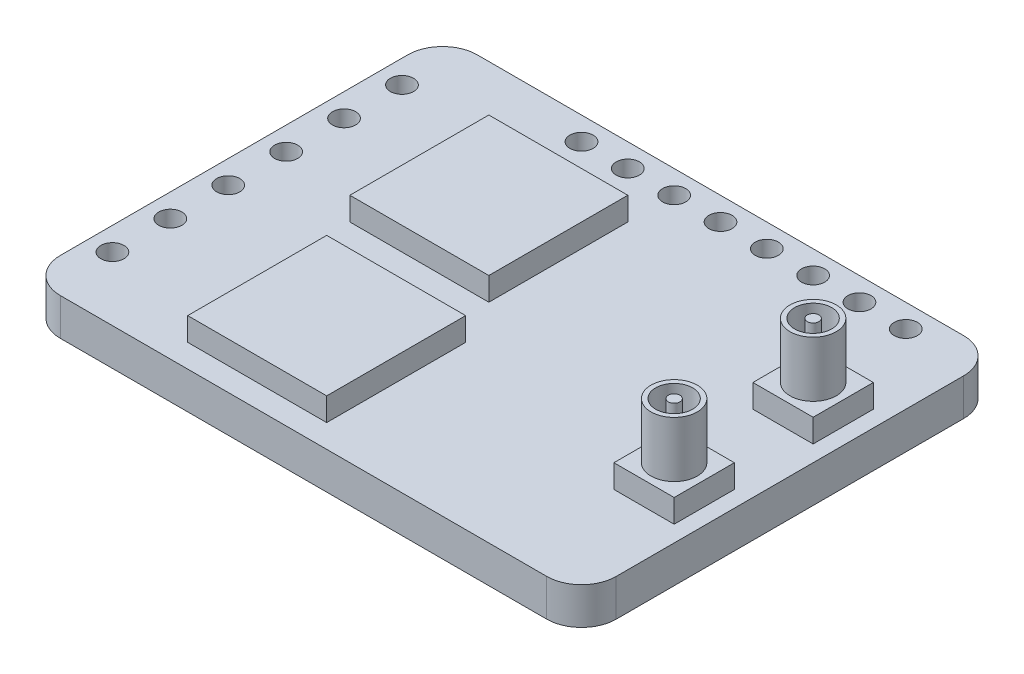
SolidWorks part; units mm, degrees
material "A-Glass Fiber"
ref_plane "Front Plane" through (0, 0, 0) normal (0, 0, 1) x (1, 0, 0)
ref_plane "Top Plane" through (0, 0, 0) normal (0, 1, 0) x (1, 0, 0)
ref_plane "Right Plane" through (0, 0, 0) normal (1, 0, 0) x (0, 0, -1)
sketch "Sketch1" plane through (0, 0, 0) normal (0, 1, 0) x (1, 0, 0)
  line L0 (-12, 0) -> (12, 0) construction
  line L1 (-12, -9) -> (12, -9) construction
  line L2 (-12, -9) -> (-12, 9) construction
  line L3 (-12, 9) -> (12, 9) construction
  line L4 (12, -9) -> (12, 9) construction
  line L5 (-12, -9) -> (12, 9) construction
  line L6 (-12, 9) -> (12, -9) construction
  line L7 (-12, 7.5) -> (-12, -7.5)
  line L8 (0, 9) -> (0, -9) construction
  line L9 (12, 7.5) -> (12, -7.5)
  line L10 (-10.5, 9) -> (10.5, 9)
  line L11 (-10.5, -9) -> (10.5, -9)
  arc A0 (-12, 7.5) -> (-10.5, 9) centre (-10.5, 7.5) cw
  arc A1 (-12, -7.5) -> (-10.5, -9) centre (-10.5, -7.5) ccw
  arc A2 (12, -7.5) -> (10.5, -9) centre (10.5, -7.5) cw
  arc A3 (12, 7.5) -> (10.5, 9) centre (10.5, 7.5) ccw
  circle A4 centre (-11, 6.25) radius 0.5
  circle A5 centre (-11, 3.75) radius 0.5
  circle A6 centre (-11, 1.25) radius 0.5
  circle A7 centre (-11, -1.25) radius 0.5
  circle A8 centre (-11, -3.75) radius 0.5
  circle A9 centre (-11, -6.25) radius 0.5
  circle A10 centre (9, 8) radius 0.5
  circle A11 centre (7, 8) radius 0.5
  circle A12 centre (5, 8) radius 0.5
  circle A13 centre (3, 8) radius 0.5
  circle A14 centre (1, 8) radius 0.5
  circle A15 centre (-1, 8) radius 0.5
  circle A16 centre (-3, 8) radius 0.5
  circle A17 centre (-5, 8) radius 0.5
  point P0 (0, 0)
  dimension "D3" = 1.5
  dimension "D4" = 1
  dimension "D8" = 1
  dimension "D1" = 24
  dimension "D2" = 18
  dimension "D5" = 1
  dimension "D6" = 2.75
  dimension "D9" = 1
  dimension "D10" = 3
  dimension "D7" = 6
  dimension "D11" = 8
extrude "Boss-Extrude1" add sketch "Sketch1" along normal blind 1.6
sketch "Sketch2" plane through (0, 1.6, 0) normal (0, 1, 0) x (1, 0, 0)
  line L0 (-12, 0) -> (12, 0) construction
  line L1 (-7, 6) -> (-1, 6)
  line L2 (-7, 6) -> (-7, 0)
  line L3 (-7, 0) -> (-1, 0)
  line L4 (-1, 6) -> (-1, 0)
  line L5 (-7, 6) -> (-1, 0) construction
  line L6 (-7, 0) -> (-1, 6) construction
  line L7 (0, 9) -> (0, -9) construction
  line L8 (-6, -8) -> (0, -8)
  line L9 (-6, -8) -> (-6, -2)
  line L10 (-6, -2) -> (0, -2)
  line L11 (0, -8) -> (0, -2)
  line L12 (-6, -8) -> (0, -2) construction
  line L13 (-6, -2) -> (0, -8) construction
  point P0 (-4, 3)
  point P7 (-3, -5)
  dimension "D1" = 6
  dimension "D2" = 1
  dimension "D3" = 2
extrude "Boss-Extrude2" add sketch "Sketch2" along normal blind 1 separate body
sketch "Sketch3" plane through (0, 1.6, 0) normal (0, 1, 0) x (1, 0, 0)
  line L0 (10, 3) -> (10, -3) construction
  line L1 (10, -3) -> (12, -3) construction
  line L2 (12, 7.5) -> (12, -7.5) construction
  line L3 (12, -3) -> (12, 3) construction
  line L4 (12, 3) -> (10, 3) construction
  line L6 (0, 0) -> (12, 0) construction
  line L7 (-12, 0) -> (12, 0) construction
  circle A0 centre (10, 3) radius 1
  circle A1 centre (10, 3) radius 0.8
  circle A2 centre (10, 3) radius 0.25
  circle A3 centre (10, -3) radius 1
  circle A4 centre (10, -3) radius 0.8
  circle A5 centre (10, -3) radius 0.25
  dimension "D1" = 2
  dimension "D2" = 1.6
  dimension "D3" = 0.5
  dimension "D4" = 2
  dimension "D5" = 1.6
  dimension "D6" = 0.5
  dimension "D7" = 6
  dimension "D8" = 3
  dimension "D9" = 2
extrude "Boss-Extrude3" add sketch "Sketch3" along normal blind 3.4 separate body contours A3 A4 | A5 | A0 A1 | A2
sketch "Sketch4" plane through (0, 1.6, 0) normal (0, 1, 0) x (1, 0, 0)
  line L1 (8.7, 4.3) -> (11.3, 4.3)
  line L2 (8.7, 4.3) -> (8.7, 1.7)
  line L3 (8.7, 1.7) -> (11.3, 1.7)
  line L4 (11.3, 4.3) -> (11.3, 1.7)
  line L5 (8.7, 4.3) -> (11.3, 1.7) construction
  line L6 (8.7, 1.7) -> (11.3, 4.3) construction
  line L7 (8.7, -1.7) -> (11.3, -1.7)
  line L8 (8.7, -1.7) -> (8.7, -4.3)
  line L9 (8.7, -4.3) -> (11.3, -4.3)
  line L10 (11.3, -1.7) -> (11.3, -4.3)
  line L11 (8.7, -1.7) -> (11.3, -4.3) construction
  line L12 (8.7, -4.3) -> (11.3, -1.7) construction
  point P0 (10, 3)
  point P6 (10, -3)
  dimension "D1" = 2.6
extrude "Boss-Extrude4" add sketch "Sketch4" along normal blind 1 separate body
combine bodies "Combine2" operation type add bodies to combine 107 109 104
combine bodies "Combine3" operation type add bodies to combine 110 105 106
